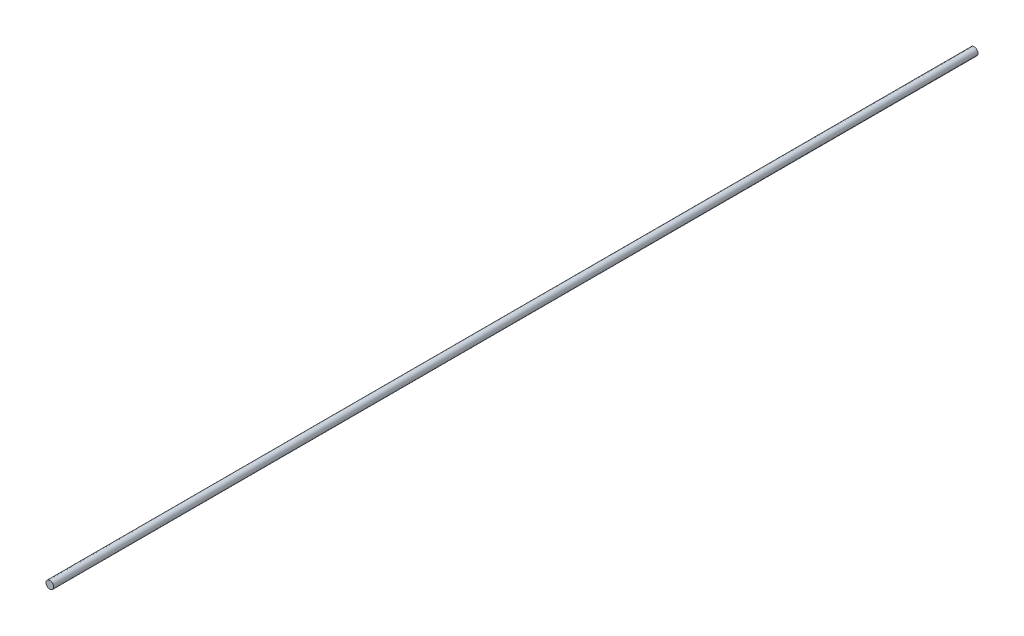
SolidWorks part; units mm, degrees
material "PLA Aero Bambu"
ref_plane "Front Plane" through (0, 0, 0) normal (0, 0, 1) x (1, 0, 0)
ref_plane "Top Plane" through (0, 0, 0) normal (0, 1, 0) x (1, 0, 0)
ref_plane "Right Plane" through (0, 0, 0) normal (1, 0, 0) x (0, 0, -1)
sketch "Sketch1" plane through (0, 0, 0) normal (0, 0, 1) x (1, 0, 0)
  circle A0 centre (0, 0) radius 1
  dimension "D1" = 2
extrude "Boss-Extrude1" add sketch "Sketch1" along normal blind 241.88
